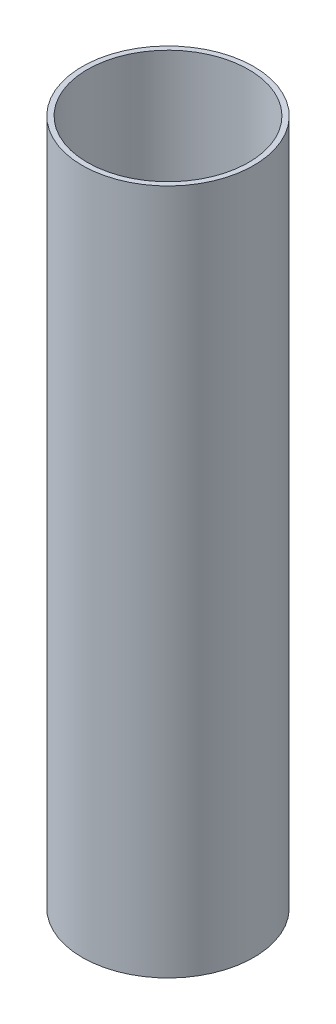
SolidWorks part; units mm, degrees
material "AISI Type 316L stainless steel"
ref_plane "Front Plane" through (0, 0, 0) normal (0, 0, 1) x (1, 0, 0)
ref_plane "Top Plane" through (0, 0, 0) normal (0, 1, 0) x (1, 0, 0)
ref_plane "Right Plane" through (0, 0, 0) normal (1, 0, 0) x (0, 0, -1)
sketch "Sketch1" plane through (0, 0, 0) normal (0, 1, 0) x (1, 0, 0)
  circle A0 centre (0, 0) radius 6.35
  circle A1 centre (0, 0) radius 5.969
  dimension "D1" = 12.7
  dimension "D2" = 0.381
extrude "Boss-Extrude1" add sketch "Sketch1" along normal blind 50.8
